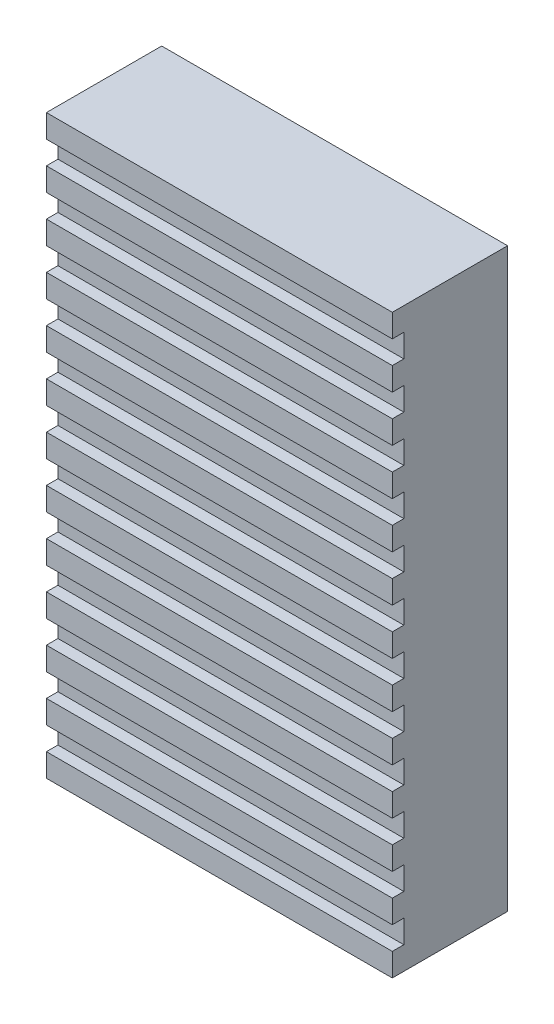
SolidWorks part; units mm, degrees
ref_plane "Front Plane" through (0, 0, 0) normal (0, 0, 1) x (1, 0, 0)
ref_plane "Top Plane" through (0, 0, 0) normal (0, 1, 0) x (1, 0, 0)
ref_plane "Right Plane" through (0, 0, 0) normal (1, 0, 0) x (0, 0, -1)
sketch "Sketch1" plane through (0, 0, 0) normal (0, 0, 1) x (1, 0, 0)
  line L1 (0, 0) -> (-30, 0)
  line L2 (0, 0) -> (0, -50)
  line L3 (0, -50) -> (-30, -50)
  line L4 (-30, 0) -> (-30, -50)
  dimension "D1" = 30
  dimension "D2" = 50
extrude "Boss-Extrude1" add sketch "Sketch1" along normal blind 10
sketch "Sketch2" plane through (0, 0, 10) normal (0, 0, 1) x (1, 0, 0)
  line L0 (-30, -2) -> (0, -2)
  line L1 (-30, 0) -> (-30, -50) construction
  line L2 (0, -50) -> (0, 0) construction
  line L3 (0, 0) -> (-30, 0) construction
  line L4 (-30, -4) -> (0, -4)
  line L5 (-30, -4) -> (-30, -2)
  line L6 (0, -2) -> (0, -4)
  line L7 (-30, -8) -> (0, -8)
  line L8 (-30, -8) -> (-30, -6)
  line L9 (-30, -6) -> (0, -6)
  line L10 (0, -6) -> (0, -8)
  line L11 (-30, -12) -> (0, -12)
  line L12 (-30, -12) -> (-30, -10)
  line L13 (-30, -10) -> (0, -10)
  line L14 (0, -10) -> (0, -12)
  line L15 (-30, -16) -> (0, -16)
  line L16 (-30, -16) -> (-30, -14)
  line L17 (-30, -14) -> (0, -14)
  line L18 (0, -14) -> (0, -16)
  line L19 (-30, -20) -> (0, -20)
  line L20 (-30, -20) -> (-30, -18)
  line L21 (-30, -18) -> (0, -18)
  line L22 (0, -18) -> (0, -20)
  line L23 (-30, -24) -> (0, -24)
  line L24 (-30, -24) -> (-30, -22)
  line L25 (-30, -22) -> (0, -22)
  line L26 (0, -22) -> (0, -24)
  line L27 (-30, -28) -> (0, -28)
  line L28 (-30, -28) -> (-30, -26)
  line L29 (-30, -26) -> (0, -26)
  line L30 (-30, -8) -> (0, -8) [skipped]
  line L31 (-30, -10) -> (0, -10) [skipped]
  line L32 (-30, -12) -> (0, -12) [skipped]
  line L33 (-30, -14) -> (0, -14) [skipped]
  line L34 (-30, -16) -> (0, -16) [skipped]
  line L35 (-30, -18) -> (0, -18) [skipped]
  line L36 (-30, -20) -> (0, -20) [skipped]
  line L37 (-30, -22) -> (0, -22) [skipped]
  line L38 (-30, -24) -> (0, -24) [skipped]
  line L39 (-30, -26) -> (0, -26) [skipped]
  line L40 (-30, -28) -> (0, -28) [skipped]
  line L41 (-30, -6) -> (0, -6) [skipped]
  line L42 (0, -26) -> (0, -28)
  line L43 (-30, -32) -> (0, -32)
  line L44 (-30, -32) -> (-30, -30)
  line L45 (-30, -30) -> (0, -30)
  line L46 (0, -30) -> (0, -32)
  line L47 (-30, -36) -> (0, -36)
  line L48 (-30, -36) -> (-30, -34)
  line L49 (-30, -34) -> (0, -34)
  line L50 (0, -34) -> (0, -36)
  line L51 (-30, -40) -> (0, -40)
  line L52 (-30, -40) -> (-30, -38)
  line L53 (-30, -38) -> (0, -38)
  line L54 (0, -38) -> (0, -40)
  line L55 (-30, -44) -> (0, -44)
  line L56 (-30, -44) -> (-30, -42)
  line L57 (-30, -42) -> (0, -42)
  line L58 (0, -42) -> (0, -44)
  line L59 (-30, -48) -> (0, -48)
  line L60 (-30, -48) -> (-30, -46)
  line L61 (-30, -46) -> (0, -46)
  line L62 (0, -46) -> (0, -48)
  dimension "D1" = 2
  dimension "D3" = 12
  dimension "D2" = 14
extrude "Cut-Extrude3" cut sketch "Sketch2" against normal blind 1
sketch "Sketch3" plane through (0, 0, 10) normal (0, 0, 1) x (1, 0, 0)
  line L0 (-30, 0) -> (-30, -50) construction
  line L1 (-30, -50) -> (-30, -25) construction
  line L2 (-30, -25) -> (27.6959, -25) construction
